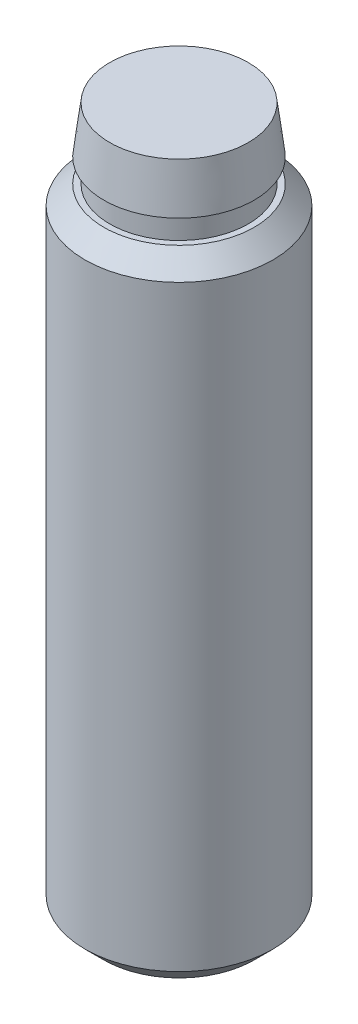
SolidWorks part; units mm, degrees
ref_plane "Face" through (0, 0, 0) normal (0, 0, 1) x (1, 0, 0)
ref_plane "Dessus" through (0, 0, 0) normal (0, 1, 0) x (1, 0, 0)
ref_plane "Droite" through (0, 0, 0) normal (1, 0, 0) x (0, 0, -1)
sketch "Esquisse1" plane through (0, 0, 0) normal (0, 0, 1) x (1, 0, 0)
  line L0 (2.95, 28) -> (3.2, 28)
  line L1 (0, 0) -> (4, 0)
  line L3 (3.2, 27) -> (4, 26.2)
  line L4 (4, 26.2) -> (4, 0)
  line L5 (0, 30) -> (2.95, 30)
  line L6 (2.95, 30) -> (3.2, 28)
  line L7 (2.95, 28) -> (2.95, 27)
  line L8 (2.95, 27) -> (3.2, 27)
  line L9 (0, 0) -> (0, 30)
  line L10 (0, -1.3668) -> (0, 32.8668) construction
  dimension "D1" = 4
  dimension "D2" = 2.95
  dimension "D3" = 2
  dimension "D6" = 30
  dimension "D7" = 1
  dimension "D8" = 3.2
  dimension "D9" = 45
  dimension "D10" = 2.95
revolve "Base-Révolution" add sketch "Esquisse1"
cosmetic thread "Représentation de filetage1"
chamfer "Chanfrein1" distance 0.8 angle 45
